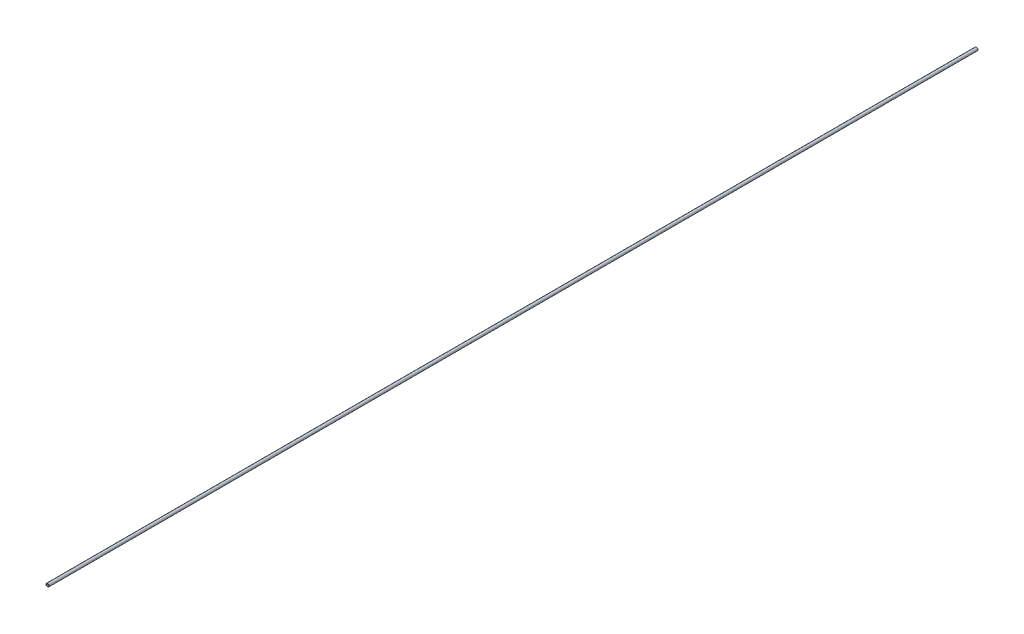
SolidWorks part; units mm, degrees
ref_plane "Front" through (0, 0, 0) normal (0, 0, 1) x (1, 0, 0)
ref_plane "Top" through (0, 0, 0) normal (0, 1, 0) x (1, 0, 0)
ref_plane "Right" through (0, 0, 0) normal (1, 0, 0) x (0, 0, -1)
sketch "Sketch1" plane through (0, 0, 0) normal (0, 0, 1) x (1, 0, 0)
  circle A0 centre (0, 0) radius 1.6
  circle A1 centre (0, 0) radius 2.5
extrude "Boss-Extrude1" add sketch "Sketch1" along normal blind 1000
sketch "Sketch2" plane through (0, 0, 1000) normal (0, 0, 1) x (1, 0, 0)
  circle A0 centre (0, 0) radius 1.6
  circle A1 centre (0, 0) radius 2.5
extrude "Boss-Extrude2" add sketch "Sketch2" along normal blind 500
